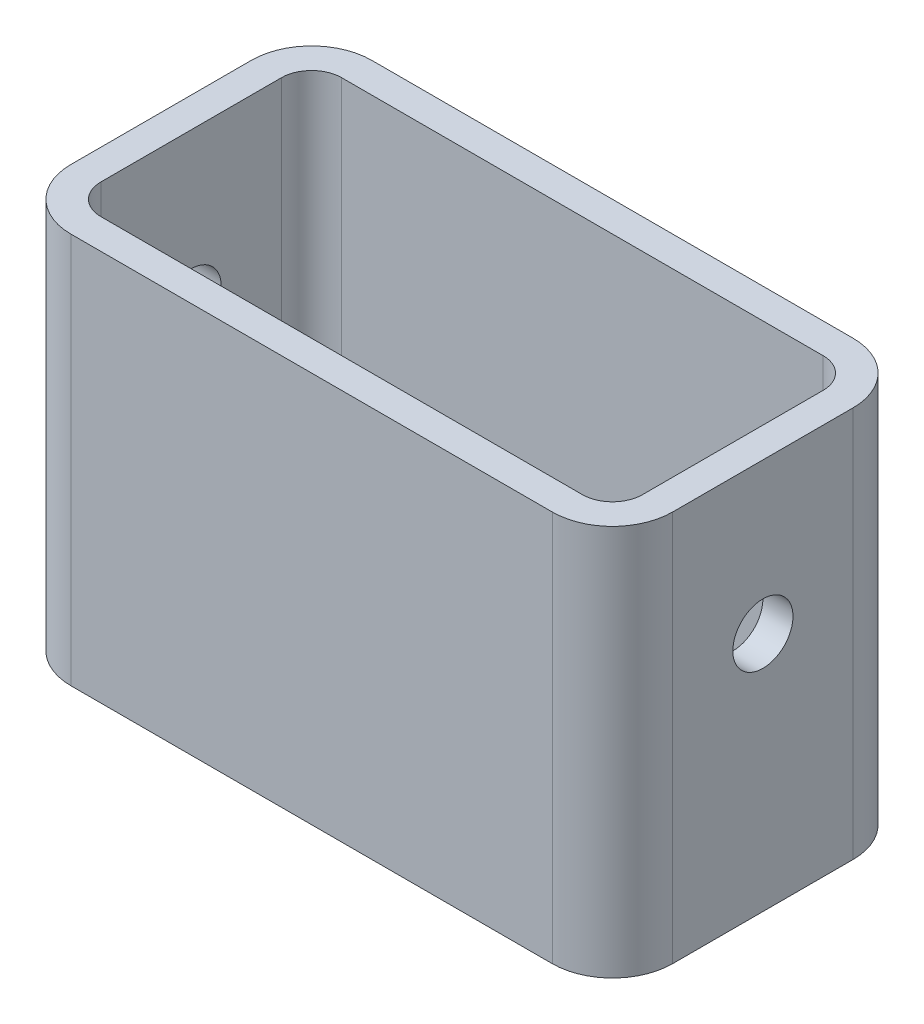
SolidWorks part; units mm, degrees
ref_plane "Front Plane" through (0, 0, 0) normal (0, 0, 1) x (1, 0, 0)
ref_plane "Top Plane" through (0, 0, 0) normal (0, 1, 0) x (1, 0, 0)
ref_plane "Right Plane" through (0, 0, 0) normal (1, 0, 0) x (0, 0, -1)
sketch "Sketch2" plane through (0, 0, 0) normal (0, 0, 1) x (1, 0, 0)
  line L1 (0, 0) -> (100, 0)
  line L2 (0, 0) -> (0, 65)
  line L3 (0, 65) -> (100, 65)
  line L4 (100, 0) -> (100, 65)
  dimension "D1" = 100
  dimension "D2" = 65
extrude "Boss-Extrude1" add sketch "Sketch2" along normal blind 50
fillet "Fillet1" radius 10 4 edges at (0, 32.5, 0) (100, 32.5, 0) (0, 32.5, 50) (100, 32.5, 50)
shell "Shell1" thickness 5
sketch "Sketch3" plane through (100, 0, 0) normal (1, 0, 0) x (0, 0, -1)
  line L0 (-50, 0) -> (-50, 65) construction
  line L1 (-40, 0) -> (-10, 0) construction
  circle A0 centre (-25, 40) radius 5
  dimension "D1" = 10
  dimension "D2" = 25
  dimension "D3" = 40
extrude "Cut-Extrude1" cut sketch "Sketch3" against normal through all
